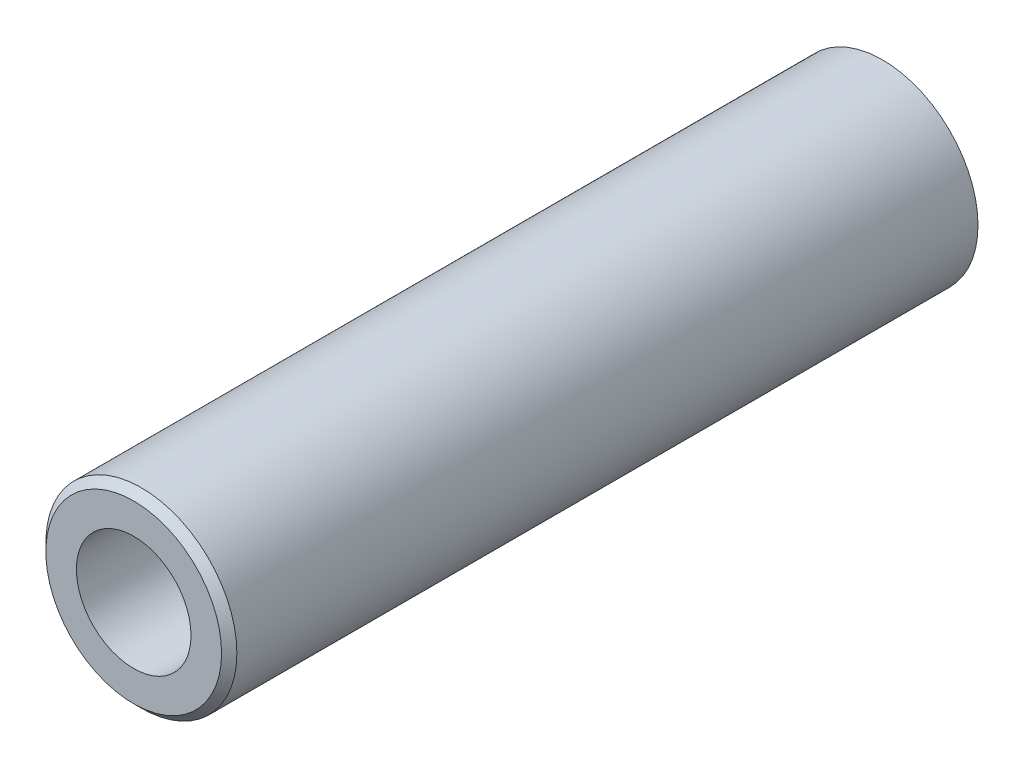
SolidWorks part; units mm, degrees
ref_plane "Front Plane" through (0, 0, 0) normal (0, 0, 1) x (1, 0, 0)
ref_plane "Top Plane" through (0, 0, 0) normal (0, 1, 0) x (1, 0, 0)
ref_plane "Right Plane" through (0, 0, 0) normal (1, 0, 0) x (0, 0, -1)
sketch "Sketch1" plane through (0, 0, 0) normal (0, 0, 1) x (1, 0, 0)
  circle A0 centre (0, 0) radius 6.25
  dimension "D1" = 12.5
extrude "Extrude-Thin1" add sketch "Sketch1" along normal mid plane 49 thin thin type one direction reverse wall 2.5
chamfer "Chamfer1" distance 0.5 angle 45 1 edges at (6.25, 0, 24.5)
